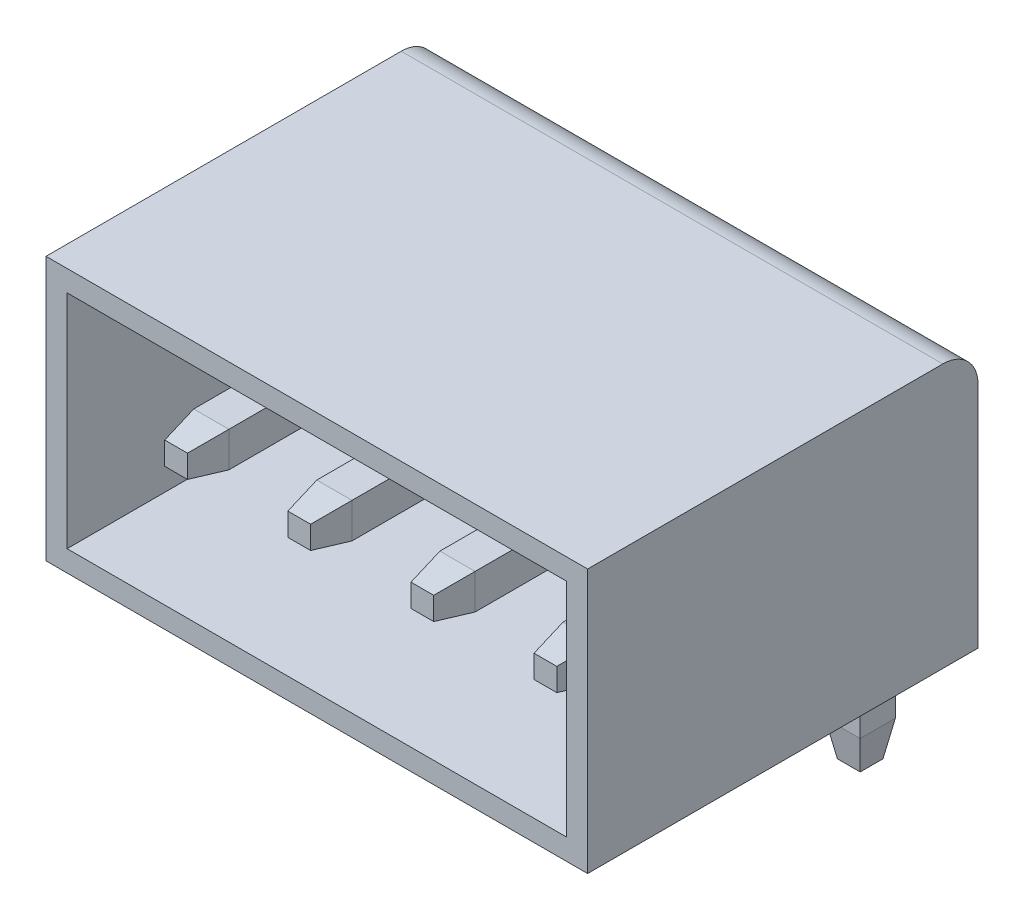
SolidWorks part; units mm, degrees
ref_plane "Front" through (0, 0, 0) normal (0, 0, 1) x (1, 0, 0)
ref_plane "Top" through (0, 0, 0) normal (0, 1, 0) x (1, 0, 0)
ref_plane "Right" through (0, 0, 0) normal (1, 0, 0) x (0, 0, -1)
sketch "Sketch1" plane through (0, 0, 0) normal (1, 0, 0) x (0, 0, -1)
  line L0 (0, 0) -> (11.1, 0)
  line L1 (11.1, 0) -> (11.1, 7.5)
  line L2 (11.1, 7.5) -> (0, 7.5)
  line L3 (0, 7.5) -> (0, 0)
  dimension "D1" = 11.1
  dimension "D2" = 7.5
extrude "Main Base" add sketch "Sketch1" along normal blind 15.4
fillet "Fillet1" radius 1 1 edges at (7.7, 7.5, -11.1)
ref_plane "Plane1" through (12.95, 0, 0) normal (1, 0, 0) x (0, 0, -1)
sketch "Sketch7" plane through (0, 0, 0) normal (0, 0, 1) x (1, 0, 0)
  line L0 (0, 7.5) -> (0, 0) construction
  line L1 (15.4, 0) -> (0, 0) construction
  line L2 (15.4, 7.5) -> (15.4, 0) construction
  line L3 (15.4, 7.5) -> (0, 7.5) construction
  line L4 (0, 7.5) -> (0, 0)
  line L5 (15.4, 0) -> (0, 0)
  line L6 (15.4, 7.5) -> (15.4, 0)
  line L7 (15.4, 7.5) -> (0, 7.5)
  line L8 (14.8, 6.9) -> (14.8, 0.6)
  line L9 (14.8, 0.6) -> (0.6, 0.6)
  line L10 (0.6, 6.9) -> (0.6, 0.6)
  line L11 (14.8, 6.9) -> (0.6, 6.9)
  dimension "D1" = 0.6
extrude "Hole" cut sketch "Sketch7" against normal offset from surface (7.8 mm away) 3.3 contours L8 L11 L10 L9 up to face at (7.7, 3.25, -11.1)
sketch "Sketch2" plane through (12.95, 0, 0) normal (1, 0, 0) x (0, 0, -1)
  line L1 (0, 7.5) -> (0, 0) construction
  line L2 (1.25, 3.5905) -> (1.25, 2.5905)
  line L3 (9.7, 1.5905) -> (9.7, -3.5)
  line L4 (10.7, 1.7905) -> (10.7, -3.5)
  line L5 (0, 0) -> (11.1, 0) construction
  line L7 (9.7, -3.5) -> (10.7, -3.5)
  line L8 (8.7, 2.5905) -> (1.25, 2.5905)
  line L9 (8.9, 3.5905) -> (1.25, 3.5905)
  arc A1 (9.7, 1.5905) -> (8.7, 2.5905) centre (8.7, 1.5905) ccw
  arc A2 (10.7, 1.7905) -> (8.9, 3.5905) centre (8.9, 1.7905) ccw
  dimension "D1" = 1
  dimension "D2" = 1.8
  dimension "D3" = 1
  dimension "D4" = 9.7
  dimension "D5" = 3.5
  dimension "D6" = 1.25
extrude "Leg" add sketch "Sketch2" along normal mid plane 1 separate body
chamfer "Leg Bottom Chamfer" distance 1 angle 10 4 edges at (12.95, -3.5, -9.7) (13.45, -3.5, -10.2) (12.45, -3.5, -10.2) (12.95, -3.5, -10.7)
chamfer "Leg Upper Chamfer" distance 1 angle 10 4 edges at (12.45, 3.0905, -1.25) (12.95, 2.5905, -1.25) (13.45, 3.0905, -1.25) (12.95, 3.5905, -1.25)
pattern_linear "4 Leg Pattern" count 4 spacing 3.5 along (-1, 0, 0) of bodies 102
